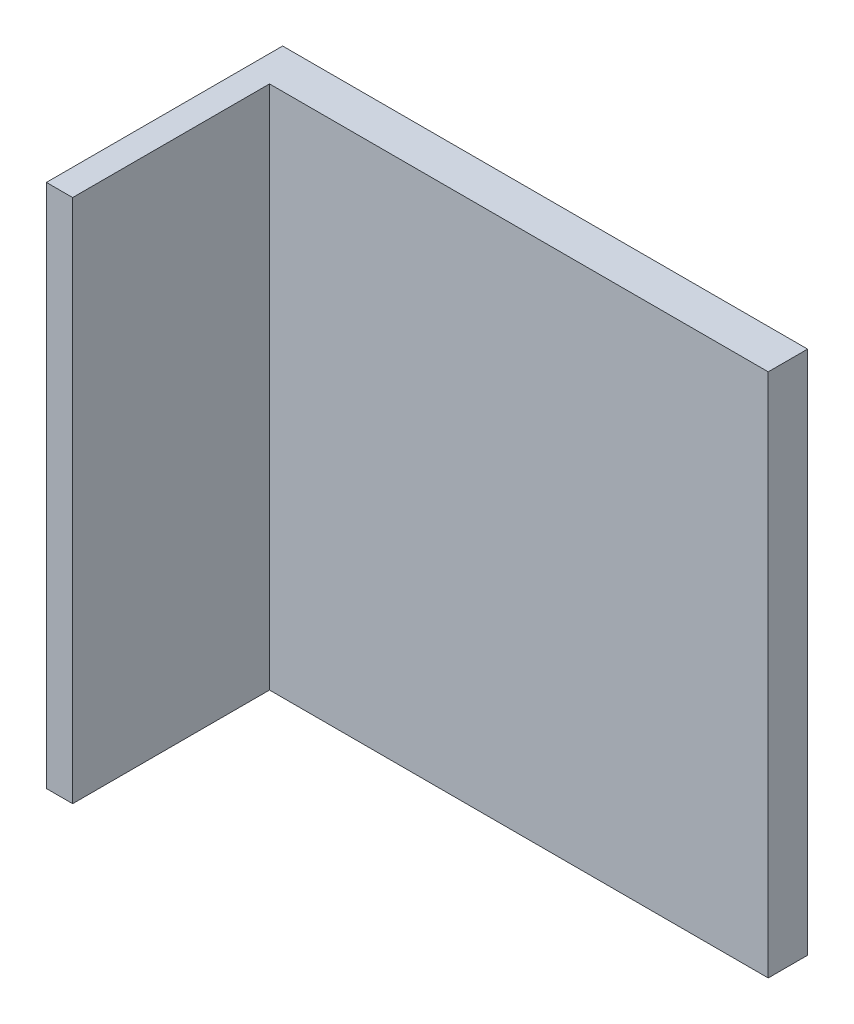
SolidWorks part; units mm, degrees
ref_plane "Front Plane" through (0, 0, 0) normal (0, 0, 1) x (1, 0, 0)
ref_plane "Top Plane" through (0, 0, 0) normal (0, 1, 0) x (1, 0, 0)
ref_plane "Right Plane" through (0, 0, 0) normal (1, 0, 0) x (0, 0, -1)
sketch "Sketch3" plane through (0, 0, 0) normal (0, 0, 1) x (1, 0, 0)
  line L1 (-75, 150) -> (125, 150)
  line L2 (-75, 150) -> (-75, -50)
  line L3 (-75, -50) -> (125, -50)
  line L4 (125, 150) -> (125, -50)
  dimension "D1" = 200
  dimension "D2" = 200
extrude "Boss-Extrude1" add sketch "Sketch3" along normal blind 15
sketch "Sketch4" plane through (0, 0, 15) normal (0, 0, 1) x (1, 0, 0)
  line L0 (-75, -50) -> (125, -50) construction
  line L1 (-75, 150) -> (-65, 150)
  line L2 (-75, 150) -> (-75, -50)
  line L3 (-75, -50) -> (-65, -50)
  line L4 (-65, 150) -> (-65, -50)
  dimension "D1" = 10
extrude "Boss-Extrude2" add sketch "Sketch4" along normal blind 75
